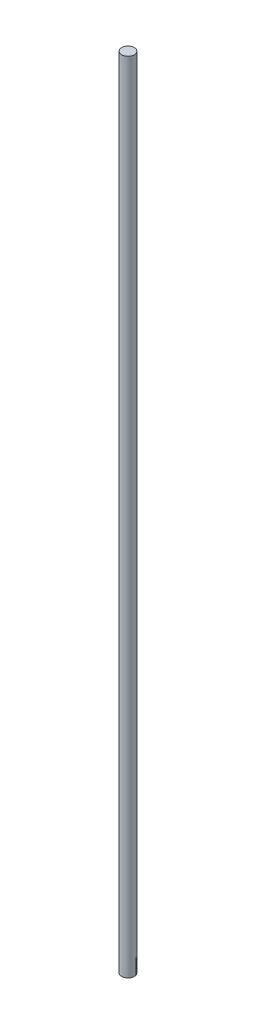
SolidWorks part; units mm, degrees
ref_plane "Ebene vorne" through (0, 0, 0) normal (0, 0, 1) x (1, 0, 0)
ref_plane "Ebene oben" through (0, 0, 0) normal (0, 1, 0) x (1, 0, 0)
ref_plane "Ebene rechts" through (0, 0, 0) normal (1, 0, 0) x (0, 0, -1)
sketch "Position" plane through (0, 0, 0) normal (0, 1, 0) x (1, 0, 0)
  circle A0 centre (14, 0) radius 1.5
  circle A1 centre (0, 0) radius 4.5
sketch "Length" plane through (0, 0, 0) normal (0, 0, 1) x (1, 0, 0)
  line L0 (0, 218) -> (0, 618)
  line L4 (14, 237) -> (14, 618)
sketch "Skizze3" plane through (0, 0, 0) normal (0, 1, 0) x (1, 0, 0)
  circle A0 centre (14, 0) radius 3
extrude "Aufsatz-Linear austragen1" add sketch "Skizze3" along normal up to vertex (618 mm away) from vertex at 237 starting at point (14, 237, 0)
sketch "Skizze4" plane through (0, 0, 0) normal (0, 1, 0) x (1, 0, 0)
  circle A0 centre (14, 0) radius 1.25
extrude "Schnitt-Linear austragen1" cut sketch "Skizze4" along normal blind 20 from vertex at 237 starting at point (14, 237, 0)
